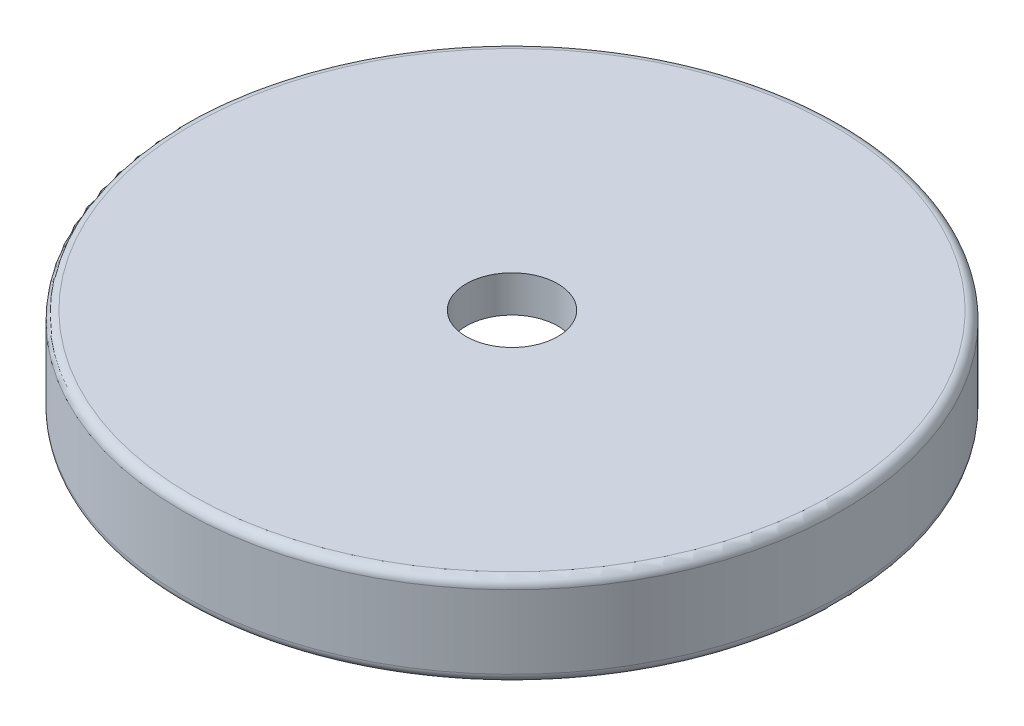
SolidWorks part; units mm, degrees
ref_plane "Front Plane" through (0, 0, 0) normal (0, 0, 1) x (1, 0, 0)
ref_plane "Top Plane" through (0, 0, 0) normal (0, 1, 0) x (1, 0, 0)
ref_plane "Right Plane" through (0, 0, 0) normal (1, 0, 0) x (0, 0, -1)
sketch "Sketch1" plane through (0, 0, 0) normal (0, 1, 0) x (1, 0, 0)
  circle A2 centre (0, 0) radius 18
  circle A3 centre (0, 0) radius 2.5
  dimension "D1" = 36
extrude "Boss-Extrude3" add sketch "Sketch1" along normal blind 2
sketch "Sketch3" plane through (0, 0, 0) normal (0, -1, 0) x (1, 0, 0)
  circle A0 centre (0, 0) radius 18 construction
  circle A1 centre (0, 0) radius 18
  circle A2 centre (0, 0) radius 15
  dimension "D1" = 3
extrude "Boss-Extrude4" add sketch "Sketch3" along normal blind 3
sketch "Sketch4" plane through (0, 0, 0) normal (0, 0, 1) x (1, 0, 0)
  line L0 (18, 0) -> (-18, 0) construction
  line L1 (18, 0) -> (-18, 0) construction
  line L2 (18, 0) -> (15, 0) construction
  line L3 (15, 0) -> (15, -2)
  arc A0 (15, -2) -> (15, 0) centre (15, -1) ccw
sketch "Sketch5" plane through (0, 0, 0) normal (0, 0, 1) x (1, 0, 0)
  line L0 (0, 0) -> (0, 4.4767) construction
  line L1 (18, 0) -> (-18, 0) construction
revolve "Cut-Revolve1" cut sketch "Sketch4" angle 360 about L0
fillet "Fillet1" radius 0.5 1 edges at (0, -2, -15)
fillet "Fillet2" radius 0.5 1 edges at (0, -3, -18)
fillet "Fillet3" radius 0.5 1 edges at (0, 2, 18)
fillet "Fillet4" radius 0.1 1 edges at (0, -3, -15)
